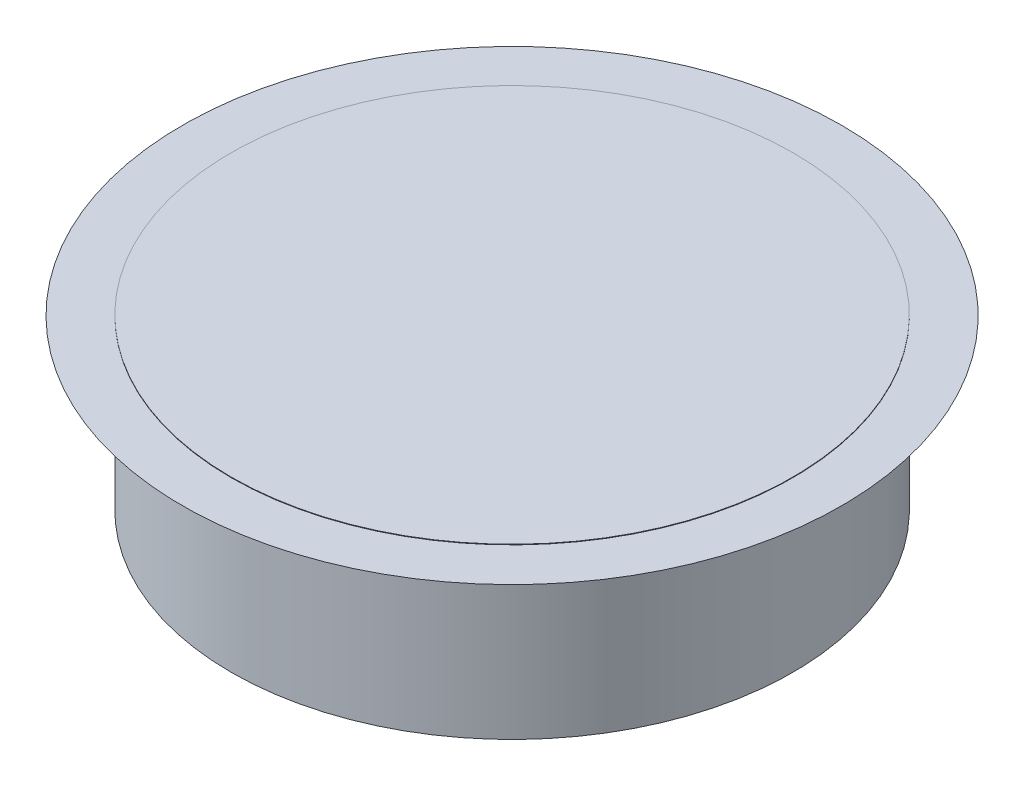
SolidWorks part; units mm, degrees
material "Custom Plastic"
ref_plane "Front Plane" through (0, 0, 0) normal (0, 0, 1) x (1, 0, 0)
ref_plane "Top Plane" through (0, 0, 0) normal (0, 1, 0) x (1, 0, 0)
ref_plane "Right Plane" through (0, 0, 0) normal (1, 0, 0) x (0, 0, -1)
sketch "Sketch1" plane through (0, 0, 0) normal (0, 0, 1) x (1, 0, 0)
  line L0 (0, 0) -> (0, 38.7866) construction
  line L1 (0, 0) -> (-12.7, 0)
  line L2 (-12.7, 0) -> (-12.7, 6.35)
  line L3 (-12.7, 6.35) -> (-14.8997, 7.62)
  line L4 (-14.8997, 7.62) -> (0, 7.62)
  line L5 (0, 7.62) -> (0, 0)
  dimension "D1" = 12.7
  dimension "D2" = 7.62
  dimension "D3" = 6.35
  dimension "D4" = 30
revolve "Revolve1" add sketch "Sketch1" angle 360 about L0
sketch "Sketch2" plane through (0, 7.62, 0) normal (0, 1, 0) x (1, 0, 0)
  circle A0 centre (0, 0) radius 12.7
  dimension "D1" = 25.4
extrude "Boss-Extrude1" add sketch "Sketch2" along normal blind 0.0254
